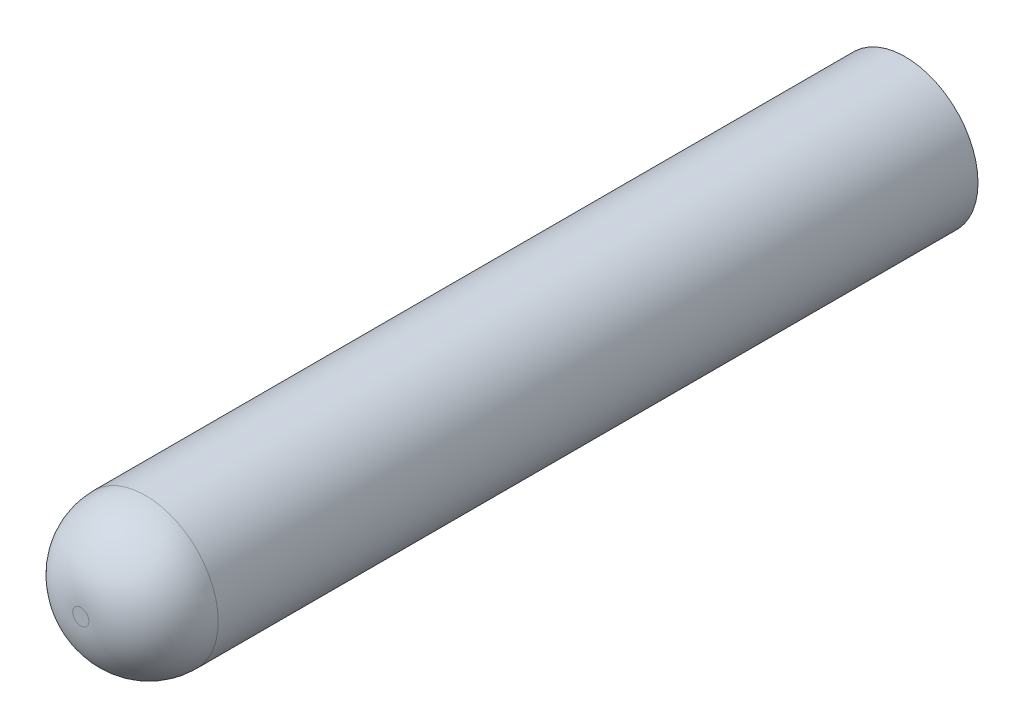
SolidWorks part; units mm, degrees
ref_plane "Front Plane" through (0, 0, 0) normal (0, 0, 1) x (1, 0, 0)
ref_plane "Top Plane" through (0, 0, 0) normal (0, 1, 0) x (1, 0, 0)
ref_plane "Right Plane" through (0, 0, 0) normal (1, 0, 0) x (0, 0, -1)
sketch "草图1" plane through (0, 0, 0) normal (0, 0, 1) x (1, 0, 0)
  circle A0 centre (0, 0) radius 2.25
  dimension "D1" = 4.5
extrude "凸台-拉伸2" add sketch "草图1" along normal blind 25.5
sketch "草图7" plane through (0, 0, 0) normal (0, 0, 1) x (1, 0, 0)
  line L1 (1.2, -1.2) -> (-1.2, -1.2)
  line L2 (1.2, -1.2) -> (1.2, 1.2)
  line L3 (1.2, 1.2) -> (-1.2, 1.2)
  line L4 (-1.2, -1.2) -> (-1.2, 1.2)
  line L5 (1.2, -1.2) -> (-1.2, 1.2) construction
  line L6 (1.2, 1.2) -> (-1.2, -1.2) construction
  point P0 (0, 0)
  dimension "D1" = 2.4
  dimension "D2" = 2.4
extrude "切除-拉伸3" cut sketch "草图7" along normal blind 4.5 from surface at 0 starting at face at (2.25, 0, 0)
fillet "圆角2" radius 2 1 edges at (2.25, 0, 25.5)
